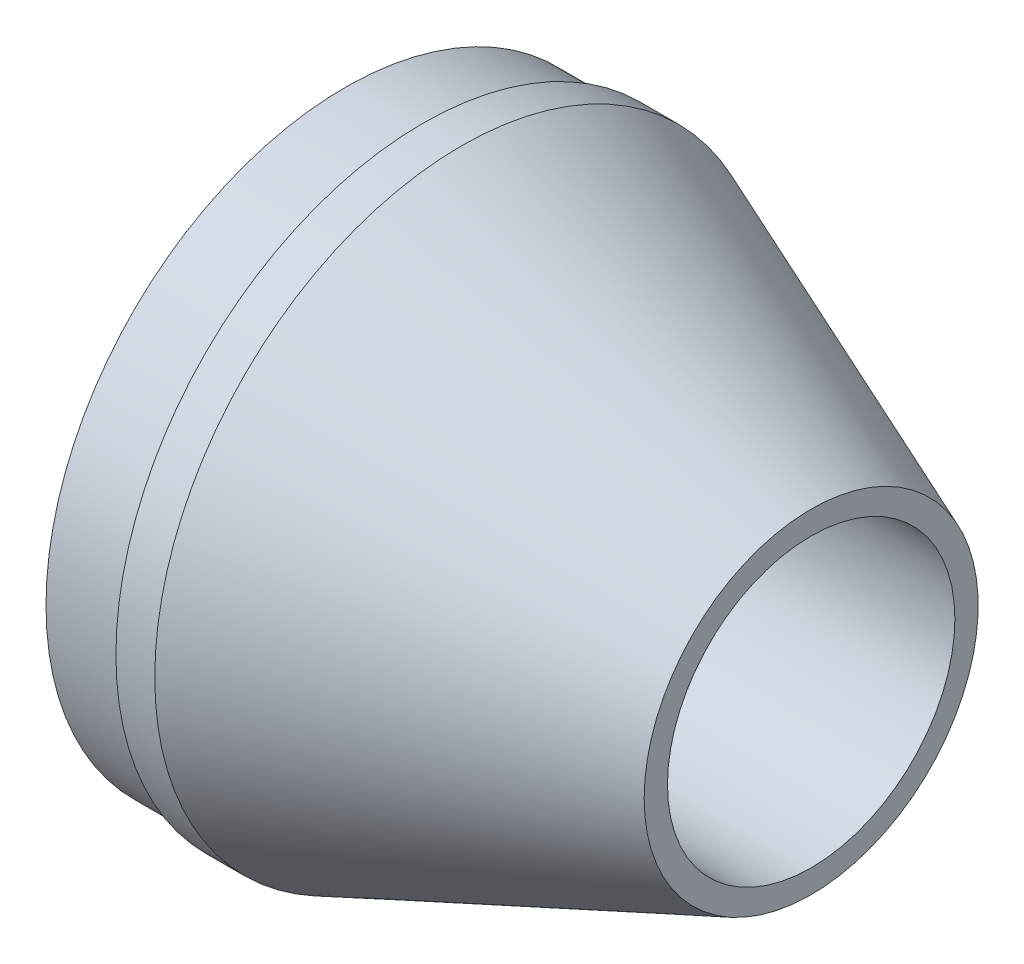
SolidWorks part; units mm, degrees
ref_plane "Plan de face" through (0, 0, 0) normal (0, 0, 1) x (1, 0, 0)
ref_plane "Plan de dessus" through (0, 0, 0) normal (0, 1, 0) x (1, 0, 0)
ref_plane "Plan de droite" through (0, 0, 0) normal (1, 0, 0) x (0, 0, -1)
sketch "Esquisse1" plane through (0, 0, 0) normal (0, 0, 1) x (1, 0, 0)
  line L0 (-28.5658, 25.2137) -> (-18.5658, 25.2137)
  line L1 (-18.5658, 25.2137) -> (-18.5658, 26.2137)
  line L2 (-18.5658, 26.2137) -> (-13.5658, 26.2137)
  line L3 (-13.5658, 26.2137) -> (31.4342, 8.2137)
  line L4 (-15.5658, 5.2137) -> (31.4342, 5.2137)
  line L7 (31.4342, 5.2137) -> (31.4342, 8.2137)
  line L8 (-15.5658, 5.2137) -> (-15.5658, 7.2137)
  line L9 (-15.5658, 7.2137) -> (-28.5658, 7.2137)
  line L10 (-28.5658, 7.2137) -> (-28.5658, 25.2137)
  line L11 (-43.5458, -13.2863) -> (46.0454, -13.2863) construction
  dimension "D1" = 10
  dimension "D2" = 5
  dimension "D3" = 1
  dimension "D4" = 3
  dimension "D5" = 38.5
  dimension "D6" = 20.5
  dimension "D7" = 13
  dimension "D8" = 2
  dimension "D9" = 60
revolve "Révolution1" add sketch "Esquisse1" angle 360 about L11
